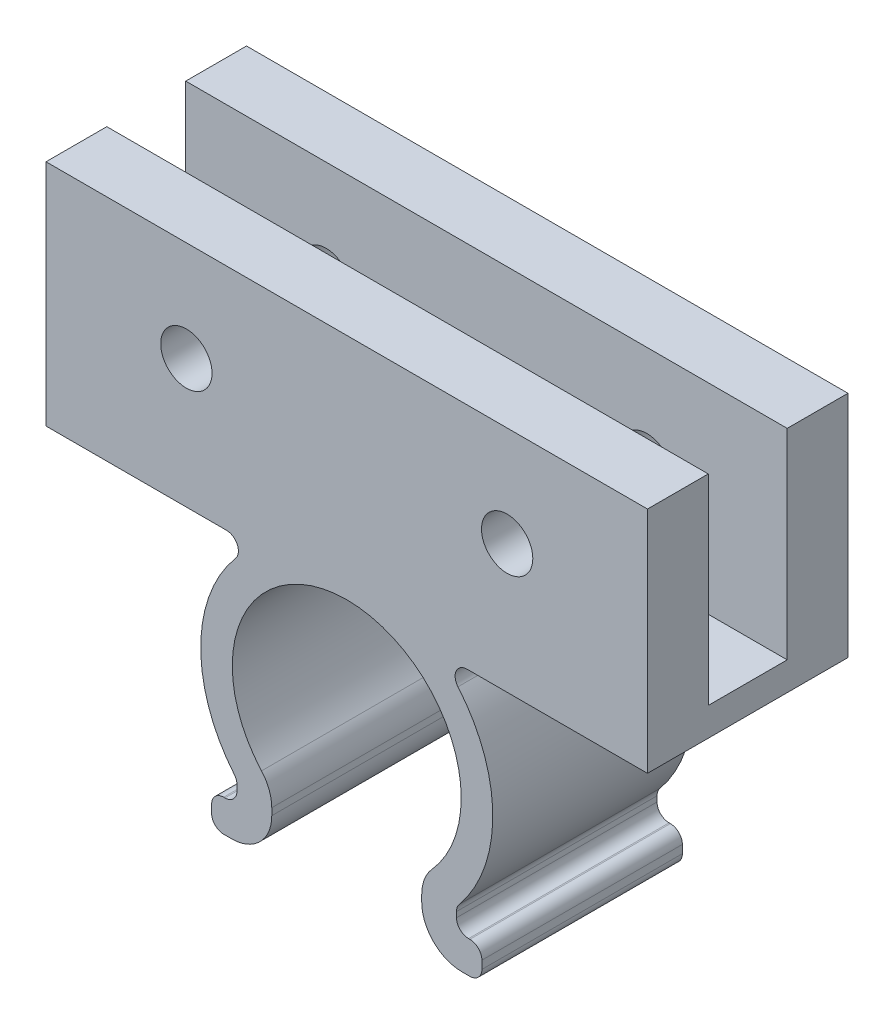
SolidWorks part; units mm, degrees
ref_plane "Front Plane" through (0, 0, 0) normal (0, 0, 1) x (1, 0, 0)
ref_plane "Top Plane" through (0, 0, 0) normal (0, 1, 0) x (1, 0, 0)
ref_plane "Right Plane" through (0, 0, 0) normal (1, 0, 0) x (0, 0, -1)
sketch "Sketch1" plane through (0, 0, 0) normal (0, 0, 1) x (1, 0, 0)
  line L7 (-4.75, -6.1232) -> (-4.75, -10.16)
  line L13 (-5.7446, 6.604) -> (-19.05, 6.604)
  line L14 (-19.05, 6.604) -> (-19.05, 21.104)
  line L15 (-19.05, 21.104) -> (19.05, 21.104)
  line L16 (19.05, 21.104) -> (19.05, 6.604)
  line L17 (19.05, 6.604) -> (5.7446, 6.604)
  line L23 (0, 0) -> (0, -13.1244) construction
  line L25 (-6.9537, -8.128) -> (-6.9537, -6.7459)
  line L27 (-4.75, -10.16) -> (-8.56, -10.16)
  line L29 (-6.9537, -8.128) -> (-8.56, -8.128)
  line L30 (-8.56, -10.16) -> (-8.56, -8.128)
  line L31 (6.9537, -8.128) -> (8.56, -8.128)
  line L32 (8.56, -10.16) -> (8.56, -8.128)
  line L33 (4.75, -10.16) -> (8.56, -10.16)
  line L34 (4.75, -6.1232) -> (4.75, -10.16)
  line L35 (6.9537, -8.128) -> (6.9537, -6.7459)
  arc A7 (-5.7446, 6.604) -> (-6.9537, -6.7459) centre (0, -0.646) ccw
  arc A8 (4.75, -6.1232) -> (-4.75, -6.1232) centre (0, -0.646) ccw
  arc A9 (6.9537, -6.7459) -> (5.7446, 6.604) centre (0, -0.646) ccw
  point P1 (0, -11.4386)
  point P17 (0, 21.104)
  dimension "D1" = 2
  dimension "D2" = 14.5
  dimension "D10" = 3.81
  dimension "D3" = 38.1
  dimension "D4" = 6.604
  dimension "D6" = 2.2037
  dimension "D7" = 4.75
  dimension "D8" = 10.16
  dimension "D9" = 14.5
  dimension "D11" = 2.032
extrude "Boss-Extrude1" add sketch "Sketch1" along normal blind 12.7
sketch "Sketch2" plane through (0, 6.604, 0) normal (0, -1, 0) x (1, 0, 0)
  line L0 (-19.05, 12.7) -> (-19.05, 0) construction
  line L1 (19.05, 12.7) -> (19.05, 0) construction
  circle A0 centre (-13.335, 6.35) radius 1.625
  circle A1 centre (13.335, 6.35) radius 1.625
  point P7 (-19.05, 6.35)
  point P11 (19.05, 6.35)
  dimension "D1" = 3.25
  dimension "D2" = 13.335
  dimension "D3" = 13.335
extrude "Cut-Extrude1" [suppressed] cut sketch "Sketch2" against normal through all
chamfer "Chamfer1" [suppressed] distance 2 angle 41
ref_plane "Plane1" through (0, 0, 6.35) normal (0, 0, 1) x (1, 0, 0)
sketch "Sketch5" plane through (-19.05, 0, 0) normal (-1, 0, 0) x (0, 0, 1)
  line L1 (3.85, 21.104) -> (8.85, 21.104)
  line L2 (3.85, 21.104) -> (3.85, 8.404)
  line L3 (3.85, 8.404) -> (8.85, 8.404)
  line L4 (8.85, 21.104) -> (8.85, 8.404)
  line L5 (12.7, 21.104) -> (0, 21.104) construction
  line L6 (6.35, -15.7321) -> (6.35, 15.7321) construction
  point P6 (6.35, 21.104)
  point P9 (0, 0)
  dimension "D1" = 12.7
  dimension "D2" = 5
extrude "Cut-Extrude2" cut sketch "Sketch5" against normal through all and the other way through all
sketch "Sketch6" plane through (0, 0, 12.7) normal (0, 0, 1) x (1, 0, 0)
  line L1 (19.05, 21.104) -> (-19.05, 21.104) construction
  circle A0 centre (-10.16, 14.754) radius 1.625
  circle A1 centre (10.16, 14.754) radius 1.625
  point P4 (-10.16, 14.8997)
  dimension "D1" = 3.25
  dimension "D2" = 6.35
  dimension "D3" = 10.16
  dimension "D4" = 10.16
extrude "Cut-Extrude3" cut sketch "Sketch6" against normal through all
fillet "Fillet1" radius 2.54 4 edges at (4.75, -6.1232, 6.35) (-4.75, -6.1232, 6.35) (4.75, -10.16, 6.35) (-4.75, -10.16, 6.35)
fillet "Fillet2" radius 0.762 10 edges at (5.7446, 6.604, 6.35) (-5.7446, 6.604, 6.35) (6.9537, -6.7459, 6.35) (6.9537, -8.128, 6.35) (8.56, -10.16, 6.35) (8.56, -8.128, 6.35) (-6.9537, -8.128, 6.35) (-6.9537, -6.7459, 6.35) (-8.56, -8.128, 6.35) (-8.56, -10.16, 6.35)
